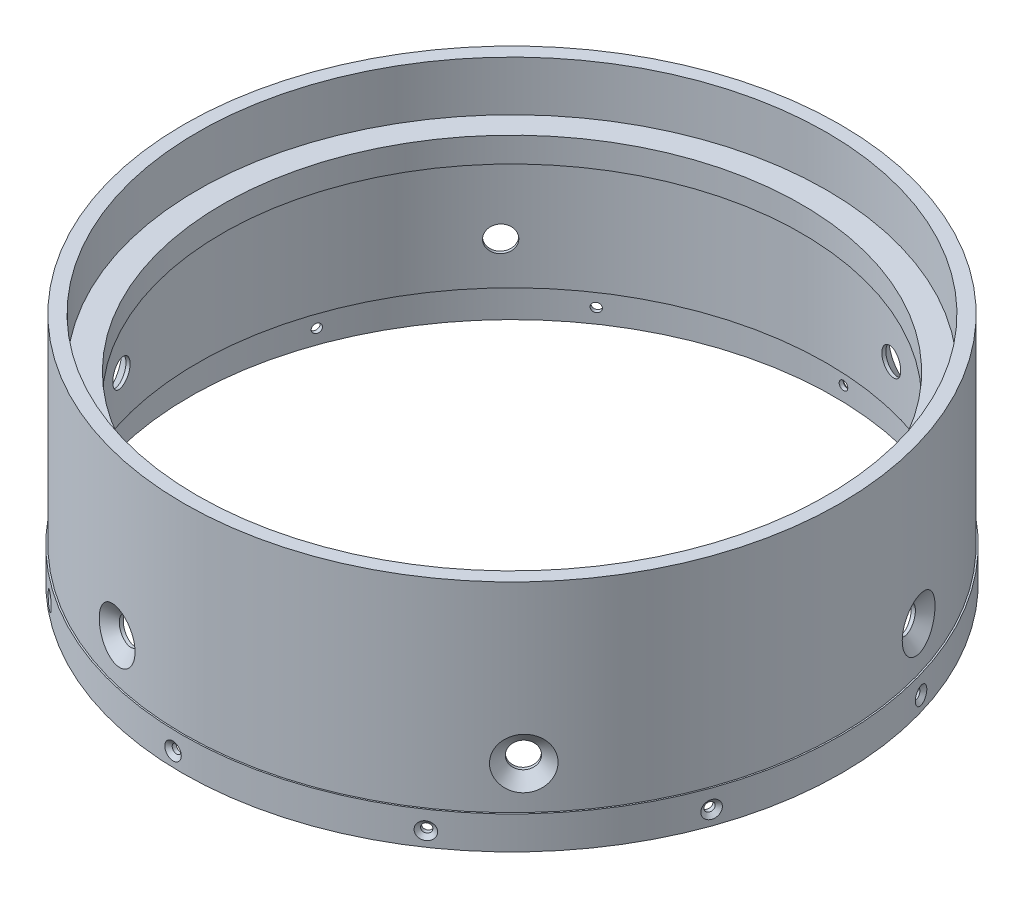
SolidWorks part; units mm, degrees
ref_plane "Front Plane" through (0, 0, 0) normal (0, 0, 1) x (1, 0, 0)
ref_plane "Top Plane" through (0, 0, 0) normal (0, 1, 0) x (1, 0, 0)
ref_plane "Right Plane" through (0, 0, 0) normal (1, 0, 0) x (0, 0, -1)
sketch "Sketch2" plane through (0, 0, 0) normal (1, 0, 0) x (0, 0, -1)
  line L0 (0, 0) -> (0, -49.6639) construction
  line L2 (79.9922, 10.5075) -> (83.439, 10.5075)
  line L3 (83.439, 10.5075) -> (83.439, -40.2925)
  line L10 (73.6422, -2.1925) -> (79.9922, -2.1925)
  line L11 (83.439, -40.2925) -> (83.82, -40.2925)
  line L12 (83.82, -40.2925) -> (83.82, -48.6745)
  line L13 (83.82, -48.6745) -> (81.9531, -48.6745)
  line L15 (81.9531, -48.6745) -> (81.9531, -40.2925)
  line L16 (79.9922, 10.5075) -> (79.9922, -2.1925)
  line L17 (81.9531, -40.2925) -> (79.9922, -40.2925)
  line L18 (79.9922, -40.2925) -> (79.9922, -8.5425)
  line L19 (79.9922, -8.5425) -> (73.6422, -8.5425)
  line L20 (73.6422, -8.5425) -> (73.6422, -2.1925)
  point P18 (0, -24.8319)
  dimension "D1" = 83.82
  dimension "D8" = 6.35
  dimension "D9" = 31.75
  dimension "D2" = 83.439
  dimension "D3" = 3.4468
  dimension "D4" = 6.35
  dimension "D5" = 12.7
  dimension "D6" = 8.382
  dimension "D7" = 1.8669
  dimension "D11" = 8.382
revolve "Revolve1" add sketch "Sketch2" angle 360 about L0
hole_wizard "CSK for #2 Flat Head Machine Screw (100)1" positions "3DSketch1" profile "Sketch3" countersink size "#2" standard "ANSI Inch"
sketch3d "3DSketch1"
  point P0 (2.4133, -45.0085, -83.7853)
sketch "Sketch3" plane through (2.4133, -45.0085, -83.7853) normal (0, 1, 0) x (-0.9996, 0, -0.0288)
  line L0 (0, 0) -> (0, 76.8792)
  line L1 (0, 76.8792) -> (1.1303, 76.2)
  line L2 (1.1303, 76.2) -> (1.1303, 0.8845)
  line L3 (1.1303, 0.8845) -> (2.1844, 0)
  line L5 (2.1844, 0) -> (0, 0)
  line L6 (-1.1303, 0.8845) -> (-2.1844, 0) construction
  line L10 (0, 76.8792) -> (-1.1303, 76.2) construction
  line L11 (0, -6.35) -> (0, 107.95) construction
  dimension "Hole Dia." = 2.2606
  dimension "Hole Depth" = 76.2
  dimension "Near C'Sink Dia." = 4.3688
  dimension "Near C'Sink Angle" = 100
  dimension "Drill Angle" = 118
pattern_circular "CirPattern1" count 10 over 360 about axis through (0, 0, 0) along (0, 1, 0) of "CSK for #2 Flat Head Machine Screw (100)1"
hole_wizard "CSK for 1/4 Flat Head Machine Screw (100)1" positions "3DSketch2" profile "Sketch4" countersink size "1/4" standard "ANSI Inch"
sketch3d "3DSketch2"
  point P0 (80.0203, -29.4878, -23.6394)
sketch "Sketch4" plane through (80.0203, -29.4878, -23.6394) normal (0, 1, 0) x (-0.2833, 0, -0.959)
  line L0 (0, 0) -> (0, 27.3611)
  line L1 (0, 27.3611) -> (3.2639, 25.4)
  line L2 (3.2639, 25.4) -> (3.2639, 2.6641)
  line L3 (3.2639, 2.6641) -> (6.4389, 0)
  line L5 (6.4389, 0) -> (0, 0)
  line L6 (-3.2639, 2.6641) -> (-6.4389, 0) construction
  line L10 (0, 27.3611) -> (-3.2639, 25.4) construction
  line L11 (0, -6.35) -> (0, 107.95) construction
  dimension "Hole Dia." = 6.5278
  dimension "Hole Depth" = 25.4
  dimension "Near C'Sink Dia." = 12.8778
  dimension "Near C'Sink Angle" = 100
  dimension "Drill Angle" = 118
pattern_circular "CirPattern2" count 6 over 360 about axis through (0, 0, 0) along (0, 1, 0) of "CSK for 1/4 Flat Head Machine Screw (100)1"
